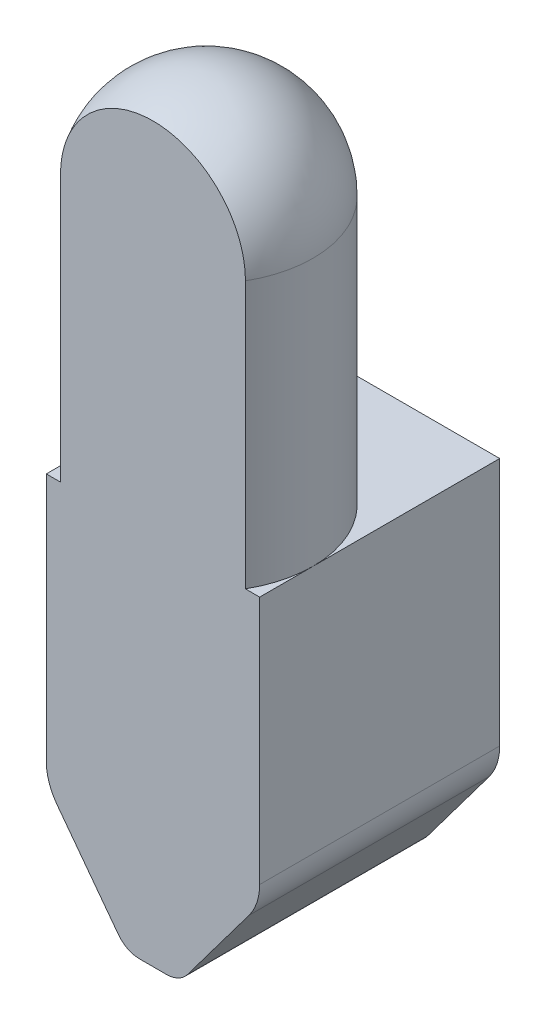
SolidWorks part; units mm, degrees
ref_plane "Спереди" through (0, 0, 0) normal (0, 0, 1) x (1, 0, 0)
ref_plane "Сверху" through (0, 0, 0) normal (0, 1, 0) x (1, 0, 0)
ref_plane "Справа" through (0, 0, 0) normal (1, 0, 0) x (0, 0, -1)
sketch "Эскиз1" plane through (0, 0, 0) normal (0, 0, 1) x (1, 0, 0)
  line L0 (0, 0) -> (0, -2) construction
  line L4 (2, 0) -> (2, 5)
  line L5 (-0.5, -2) -> (0.5, -2)
  line L6 (0.5, -2) -> (2, 0)
  line L7 (0, 0) -> (0, 5) construction
  line L8 (-2, 5) -> (2, 5)
  line L9 (-0.5, -2) -> (-2, 0)
  line L10 (-2, 0) -> (-2, 5)
  dimension "D1" = 5
  dimension "D2" = 2
  dimension "D3" = 2
  dimension "D4" = 0.5
extrude "Бобышка-Вытянуть1" add sketch "Эскиз1" against normal blind 4.5
sketch "Эскиз2" plane through (0, 5, 0) normal (0, 1, 0) x (1, 0, 0)
  line L0 (0, 0) -> (0, 1) construction
  line L1 (-1.7321, 0) -> (1.7321, 0)
  line L2 (2, 0) -> (-2, 0) construction
  arc A0 (1.7321, 0) -> (-1.7321, 0) centre (0, 1) ccw
  dimension "D1" = 1
extrude "Бобышка-Вытянуть2" add sketch "Эскиз2" along normal blind 5
sketch "Эскиз3" plane through (0, 10, 0) normal (0, 1, 0) x (1, 0, 0)
  line L0 (0, 0) -> (0, 3) construction
  line L1 (-1.7321, 0) -> (1.7321, 0) construction
  line L2 (2, 1) -> (0, 1) construction
  line L3 (-2, 1) -> (2, 1)
  arc A0 (2, 1) -> (-2, 1) centre (0, 1) ccw construction
  circle A1 centre (0, 1) radius 2
revolve "Повернуть1" add sketch "Эскиз3" angle 360 about L3
sketch "Эскиз4" plane through (0, 0, 0) normal (0, 1, 0) x (1, 0, 0)
  line L1 (-2, 0) -> (2.1075, 0)
  line L2 (-2, 0) -> (-2, -2.2741)
  line L3 (-2, -2.2741) -> (2.1075, -2.2741)
  line L4 (2.1075, 0) -> (2.1075, -2.2741)
extrude "Вырез-Вытянуть1" cut sketch "Эскиз4" against normal through all both and the other way through all
fillet "Скругление1" radius 1 2 edges at (-2, 0, -2.25) (2, 0, -2.25)
fillet "Скругление2" radius 0.5 2 edges at (-0.5, -2, -2.25) (0.5, -2, -2.25)
